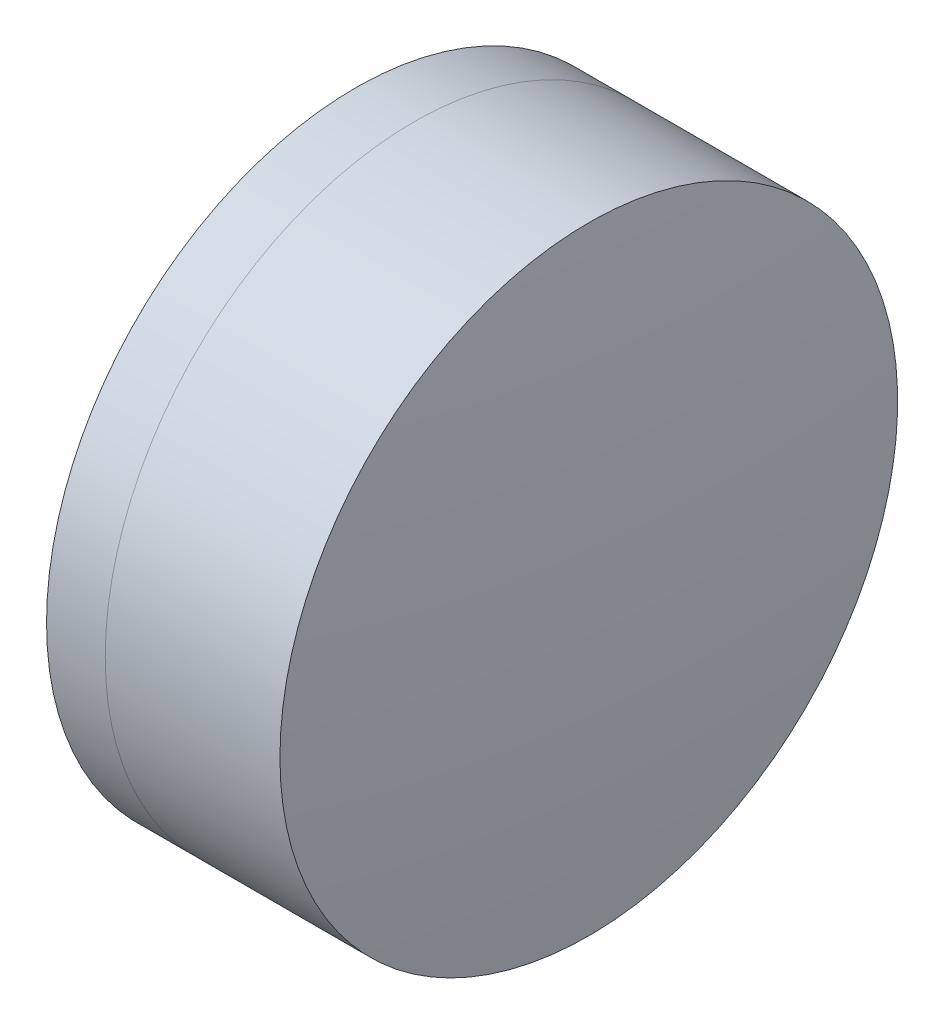
SolidWorks part; units mm, degrees
ref_plane "前视基准面" through (0, 0, 0) normal (0, 0, 1) x (1, 0, 0)
ref_plane "上视基准面" through (0, 0, 0) normal (0, 1, 0) x (1, 0, 0)
ref_plane "右视基准面" through (0, 0, 0) normal (1, 0, 0) x (0, 0, -1)
sketch "草图1" plane through (0, 0, 0) normal (0, 1, 0) x (1, 0, 0)
  line L0 (124.5233, 0) -> (646.9917, 0) construction
  line L1 (264.3561, -4) -> (265.1162, -4)
  line L2 (264.3561, 4) -> (265.1162, 4)
  arc A0 (265.1162, -4) -> (265.1162, 4) centre (257.5031, 0) ccw
  arc A1 (264.3561, 4) -> (264.3561, -4) centre (274.6031, 0) ccw
  point P10 (263.6031, 0)
  point P11 (266.1031, 0)
  dimension "D3" = 11
  dimension "D4" = 8.6
  dimension "D1" = 4
  dimension "D2" = 4
  dimension "D5" = 2.5
revolve "旋转1" add sketch "草图1" angle 360 about L0
sketch "草图2" plane through (0, 0, 0) normal (0, 1, 0) x (1, 0, 0)
  line L0 (-0.5519, 0) -> (622.6607, 0) construction
  line L2 (265.1162, 4) -> (267.3789, 4)
  line L3 (265.1162, -4) -> (267.3789, -4)
  arc A0 (267.3789, -4) -> (267.3789, 4) centre (231.8031, 0) ccw
  arc A1 (265.1162, -4) -> (265.1162, 4) centre (257.5031, 0) ccw construction
  arc A2 (265.1162, -4) -> (265.1162, 4) centre (257.5031, 0) ccw
  point P4 (266.1031, 0)
  point P8 (267.6031, 0)
  dimension "D1" = 35.8
  dimension "D2" = 1.5
revolve "旋转3" add sketch "草图2" angle 360 about L0
